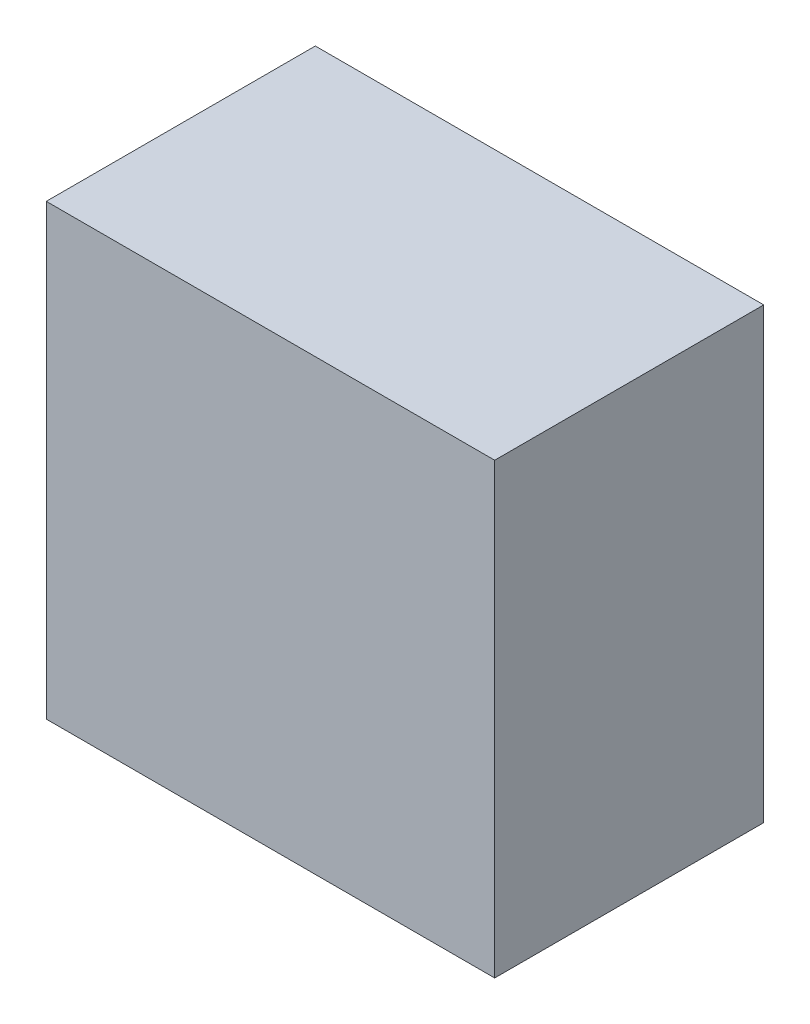
SolidWorks part; units mm, degrees
ref_plane "前基準面" through (0, 0, 0) normal (0, 0, 1) x (1, 0, 0)
ref_plane "上基準面" through (0, 0, 0) normal (0, 1, 0) x (1, 0, 0)
ref_plane "右基準面" through (0, 0, 0) normal (1, 0, 0) x (0, 0, -1)
sketch "草圖1" plane through (0, 0, 0) normal (0, 0, 1) x (1, 0, 0)
  line L0 (0, -55) -> (0, 55) construction
  line L1 (-10, 10) -> (10, 10)
  line L2 (-10, 10) -> (-10, -10)
  line L3 (-10, -10) -> (10, -10)
  line L4 (10, 10) -> (10, -10)
  line L5 (55, 0) -> (-55, 0) construction
  dimension "D1" = 20
  dimension "D2" = 20
  dimension "D3" = 10
  dimension "D4" = 10
extrude "填料-伸長1" add sketch "草圖1" along normal blind 12
sketch "草圖2" plane through (0, 0, 0) normal (0, 0, -1) x (-1, 0, 0)
  line L0 (0, 6.6) -> (0, -6.6) construction
  line L1 (-9, 9) -> (9, 9)
  line L2 (-9, 9) -> (-9, -9)
  line L3 (-9, -9) -> (9, -9)
  line L4 (9, 9) -> (9, -9)
  line L5 (6.6, 0) -> (-6.6, 0) construction
  dimension "D1" = 18
  dimension "D2" = 18
  dimension "D3" = 9
  dimension "D4" = 9
extrude "除料-伸長1" cut sketch "草圖2" against normal blind 10
